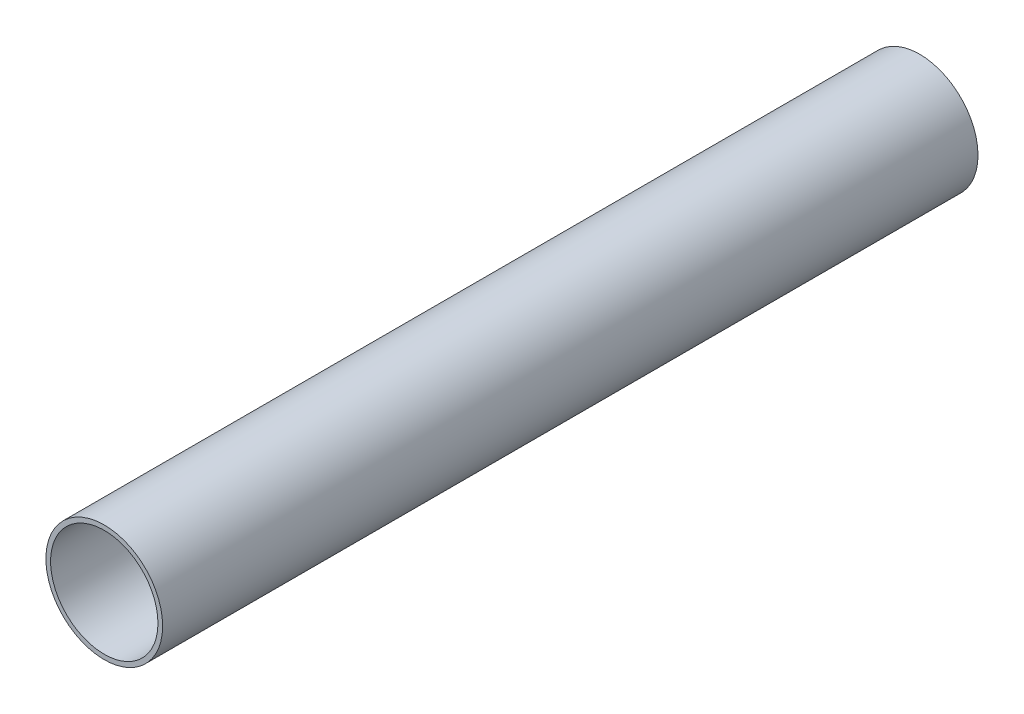
SolidWorks part; units mm, degrees
material "AISI 1020"
ref_plane "Front Plane" through (0, 0, 0) normal (0, 0, 1) x (1, 0, 0)
ref_plane "Top Plane" through (0, 0, 0) normal (0, 1, 0) x (1, 0, 0)
ref_plane "Right Plane" through (0, 0, 0) normal (1, 0, 0) x (0, 0, -1)
sketch "Sketch1" plane through (0, 0, 0) normal (0, 0, 1) x (1, 0, 0)
  circle A0 centre (0, 0) radius 25
  circle A1 centre (0, 0) radius 23
  dimension "D1" = 50
  dimension "D2" = 2
extrude "Boss-Extrude1" add sketch "Sketch1" along normal blind 349.25
